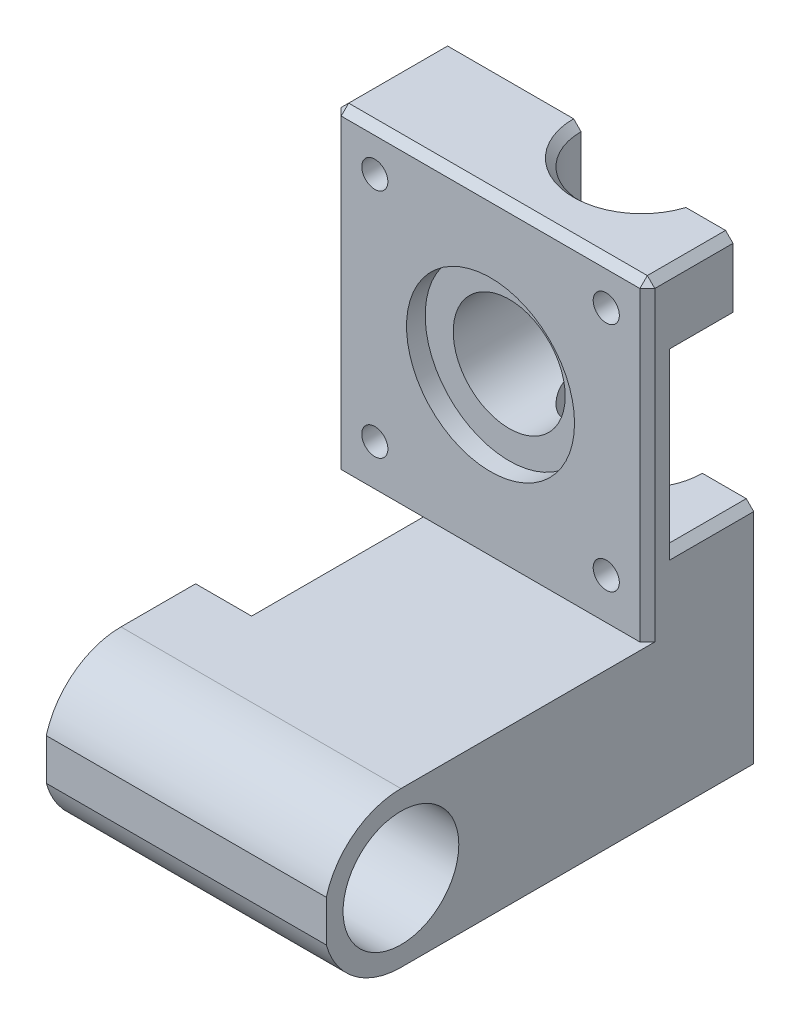
SolidWorks part; units mm, degrees
material "ABS"
ref_plane "Front Plane" through (0, 0, 0) normal (0, 0, 1) x (1, 0, 0)
ref_plane "Top Plane" through (0, 0, 0) normal (0, 1, 0) x (1, 0, 0)
ref_plane "Right Plane" through (0, 0, 0) normal (1, 0, 0) x (0, 0, -1)
sketch "Sketch1" plane through (0, 0, 0) normal (0, 1, 0) x (1, 0, 0)
  line L0 (23.125, 14.25) -> (30, 14.25)
  line L1 (0, 0) -> (30, 0)
  line L2 (0, 0) -> (0, 14.25)
  line L3 (0, 14.25) -> (6.875, 14.25)
  line L4 (30, 0) -> (30, 14.25)
  arc A1 (6.875, 14.25) -> (23.125, 14.25) centre (15, 14.25) ccw
  dimension "D1" = 14.25
  dimension "D2" = 30
extrude "Boss-Extrude1" add sketch "Sketch1" along normal blind 21
sketch "Sketch2" plane through (0, 0, 0) normal (0, -1, 0) x (1, 0, 0)
  line L0 (21.25, -14.25) -> (30, -14.25)
  line L1 (0, 0) -> (30, 0)
  line L2 (0, 0) -> (0, -14.25)
  line L3 (0, -14.25) -> (8.75, -14.25)
  line L4 (30, 0) -> (30, -14.25)
  arc A0 (21.25, -14.25) -> (8.75, -14.25) centre (15, -14.25) ccw
extrude "Boss-Extrude2" add sketch "Sketch2" along normal blind 5.75
sketch "Sketch3" plane through (0, -5.75, 0) normal (0, -1, 0) x (1, 0, 0)
  line L0 (23.25, -14.25) -> (30, -14.25)
  line L1 (0, 0) -> (30, 0)
  line L2 (0, 0) -> (0, -14.25)
  line L3 (0, -14.25) -> (6.75, -14.25)
  line L4 (30, 0) -> (30, -14.25)
  arc A0 (23.25, -14.25) -> (6.75, -14.25) centre (15, -14.25) ccw
extrude "Boss-Extrude3" add sketch "Sketch3" along normal blind 7
sketch "Sketch6" plane through (0, 0, 0) normal (-1, 0, 0) x (0, 0, 1)
  line L0 (0, 21) -> (0, -12.75) construction
  line L1 (-14.25, 21) -> (0, 21)
  line L2 (-14.25, 21) -> (-14.25, 8)
  line L3 (-14.25, 8) -> (0, 8)
  line L4 (0, 21) -> (0, 8)
  line L5 (23, 8) -> (-14.25, 8) construction
extrude "Boss-Extrude4" add sketch "Sketch6" along normal up to surface (12 mm away)
sketch "Sketch7" plane through (0, 21, 0) normal (0, 1, 0) x (1, 0, 0)
  line L0 (30, 0) -> (30, 14.25) construction
  line L1 (-12, 0) -> (30, 0)
  line L2 (-12, 0) -> (-12, 5.6216)
  line L4 (30, 0) -> (30, 5.6216)
  line L7 (-12, 5.6216) -> (-12, 14.25)
  line L8 (-12, 14.25) -> (0.7176, 14.25)
  line L12 (30, 5.6216) -> (30, 11.4778)
  line L13 (30, 11.4778) -> (24.5301, 11.4778)
  line L16 (24.5301, 11.4778) -> (22.6374, 11.4778)
  line L17 (0.7176, 14.25) -> (6.875, 14.25)
  arc A7 (6.875, 14.25) -> (22.6374, 11.4778) centre (15, 14.25) ccw
extrude "Boss-Extrude5" add sketch "Sketch7" along normal up to surface (29 mm away)
sketch "Sketch8" plane through (0, 0, 0) normal (0, 0, 1) x (1, 0, 0)
  circle A0 centre (9, 29) radius 11.25
extrude "Cut-Extrude1" cut sketch "Sketch8" against normal blind 2.5
sketch "Sketch9" plane through (0, 0, 0) normal (0, 0, 1) x (1, 0, 0)
  circle A0 centre (-6.5, 44.5) radius 1.75
  circle A1 centre (-6.5, 13.5) radius 1.75
  circle A2 centre (24.5, 13.5) radius 1.75
  circle A3 centre (24.5, 44.5) radius 1.75
  circle A5 centre (9, 29) radius 7.5
extrude "Cut-Extrude2" cut sketch "Sketch9" against normal through all
sketch "Sketch10" plane through (0, 0, 0) normal (0, 0, 1) x (1, 0, 0)
  line L1 (30, -12.75) -> (0, -12.75)
  line L2 (30, -12.75) -> (30, 8)
  line L3 (30, 8) -> (0, 8)
  line L4 (0, -12.75) -> (0, 8)
extrude "Boss-Extrude6" add sketch "Sketch10" along normal up to surface (23 mm away)
sketch "Sketch11" plane through (30, 0, 0) normal (1, 0, 0) x (0, 0, -1)
  line L0 (0, 50) -> (0, 8) construction
  line L1 (11.4778, 17.5) -> (4, 17.5)
  line L2 (11.4778, 21) -> (11.4778, 40)
  line L3 (11.4778, 40) -> (4, 40)
  line L4 (4, 17.5) -> (4, 40)
  line L5 (11.4778, 50) -> (0, 50) construction
  line L6 (11.4778, 17.5) -> (14.25, 17.5)
  line L7 (14.25, 21) -> (14.25, -12.75) construction
  line L8 (14.25, 17.5) -> (14.25, 21)
  line L9 (14.25, 21) -> (11.4778, 21)
  dimension "D1" = 22.5
  dimension "D2" = 4
  dimension "D3" = 7.4778
  dimension "D4" = 10
extrude "Cut-Extrude4" cut sketch "Sketch11" against normal blind 15
sketch "Sketch12" plane through (0, 0, 23) normal (0, 0, 1) x (1, 0, 0)
  line L0 (-7.5, -22.375) -> (-7.5, 8) construction
  line L1 (30, 8) -> (-7.5, 8)
  line L2 (30, 8) -> (30, -12.75)
  line L3 (30, -12.75) -> (-7.5, -12.75)
  line L4 (-7.5, 8) -> (-7.5, -12.75)
  line L7 (30, -12.75) -> (0, -12.75) construction
extrude "Boss-Extrude7" add sketch "Sketch12" along normal blind 20
sketch "Sketch13" plane through (30, 0, 0) normal (1, 0, 0) x (0, 0, -1)
  line L0 (-43, 8) -> (-23, -12.75) construction
  line L1 (14.25, -12.75) -> (-43, -12.75) construction
  line L2 (-23, -22.375) -> (-23, -12.75) construction
  line L3 (-43, 8) -> (0, 8) construction
  line L4 (-33, 8) -> (-43, 8)
  line L5 (-43, 8) -> (-43, -12.75)
  line L6 (-43, -12.75) -> (-33, -12.75)
  circle A0 centre (-33, -2.375) radius 7.75
  arc A1 (-33, 8) -> (-43, 0.3892) centre (-33, -2.375) ccw
  arc A2 (-43, -5.1392) -> (-33, -12.75) centre (-33, -2.375) ccw
  line M8 (0, 8) -> (-43, 8)
  line M9 (-43, 8) -> (-43, -12.75)
  line M10 (-43, -12.75) -> (14.25, -12.75)
extrude "Cut-Extrude5" cut sketch "Sketch13" against normal through all contours L0 A1 M9 | L0 A1 M8 | A0 L0 | L0 A0 | A2 M9 M10
sketch "Sketch14" plane through (0, -12.75, 0) normal (0, -1, 0) x (-1, 0, 0)
  circle A0 centre (-20.625, -15) radius 1.5
  circle A1 centre (-1.875, -15) radius 1.5
extrude "Cut-Extrude6" cut sketch "Sketch14" against normal blind 10
chamfer "Chamfer1" distance 1 angle 45 10 edges at (30, 29, 0) (30, 17.5, -9.125) (30, 40, -7.7389) (30, 28.75, -4) (-12, 29, 0) (-12, 8, -7.125) (-12, 50, -7.125) (13.5926, 50, -6.2478) (30, 50, -5.7389) (9, 50, 0)
